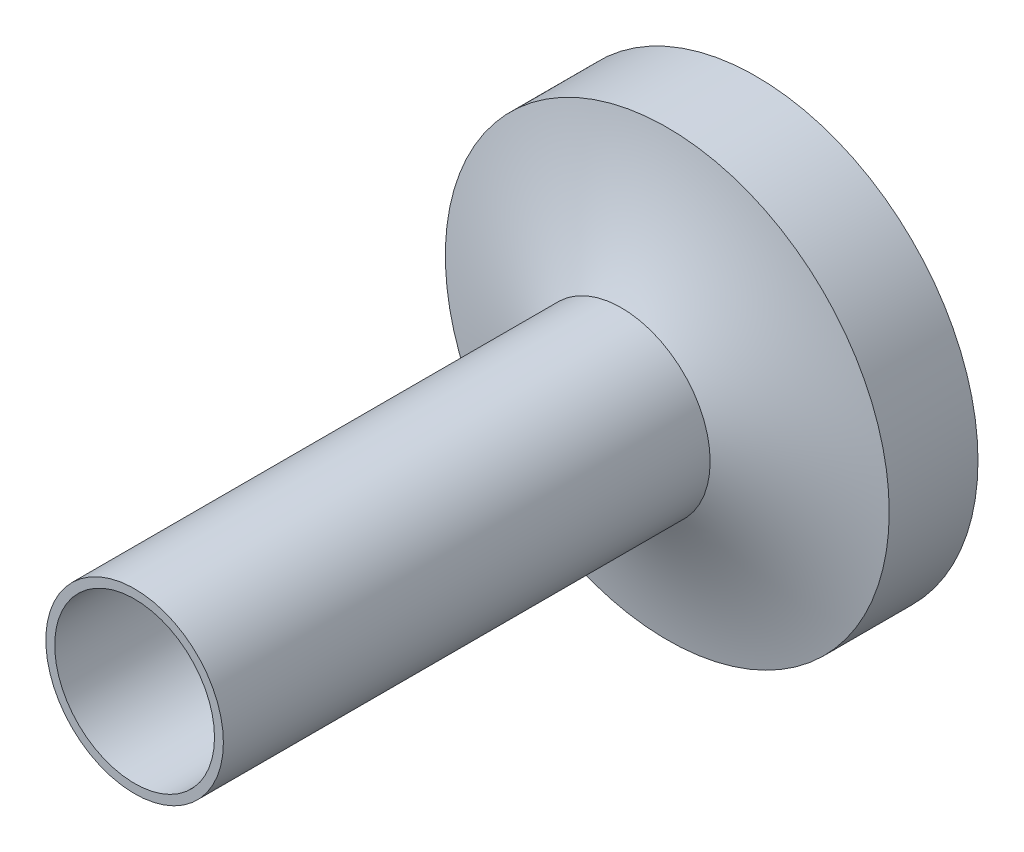
SolidWorks part; units mm, degrees
ref_plane "Alzado" through (0, 0, 0) normal (0, 0, 1) x (1, 0, 0)
ref_plane "Planta" through (0, 0, 0) normal (0, 1, 0) x (1, 0, 0)
ref_plane "Vista lateral" through (0, 0, 0) normal (1, 0, 0) x (0, 0, -1)
sketch "Croquis1" plane through (0, 0, 0) normal (0, 0, 1) x (1, 0, 0)
  circle A0 centre (0, 0) radius 2.5
  circle A1 centre (0, 0) radius 1
extrude "Saliente-Extruir1" add sketch "Croquis1" along normal blind 1
sketch "Croquis2" plane through (0, 0, 1) normal (0, 0, 1) x (1, 0, 0)
  circle A0 centre (0, 0) radius 1
extrude "Saliente-Extruir2" add sketch "Croquis2" along normal blind 6 separate body
shell "Vaciado2" thickness 0.1
sketch "Croquis3" plane through (0, 0, 0) normal (1, 0, 0) x (0, 0, -1)
  line L0 (-1.517, 1) -> (-1.1328, 1.7297) construction
  line L2 (-1.1328, 1.7297) -> (-1, 2.5) construction
  line L3 (-1, 1) -> (-7, 1) construction
  line L4 (-1, 2.5) -> (-1, 1)
  line L5 (-1, 1) -> (-1.517, 1)
  spline S0 degree 2 poles (-1.517, 1) (-1.1328, 1.7297) (-1, 2.5) knots 0 0 0 1 1 1
sketch "Croquis5" plane through (0, 0, 0) normal (1, 0, 0) x (0, 0, -1)
  line L0 (-7.0408, 0) -> (0, 0)
revolve "Revolución2" add sketch "Croquis3" angle 360 about L0
